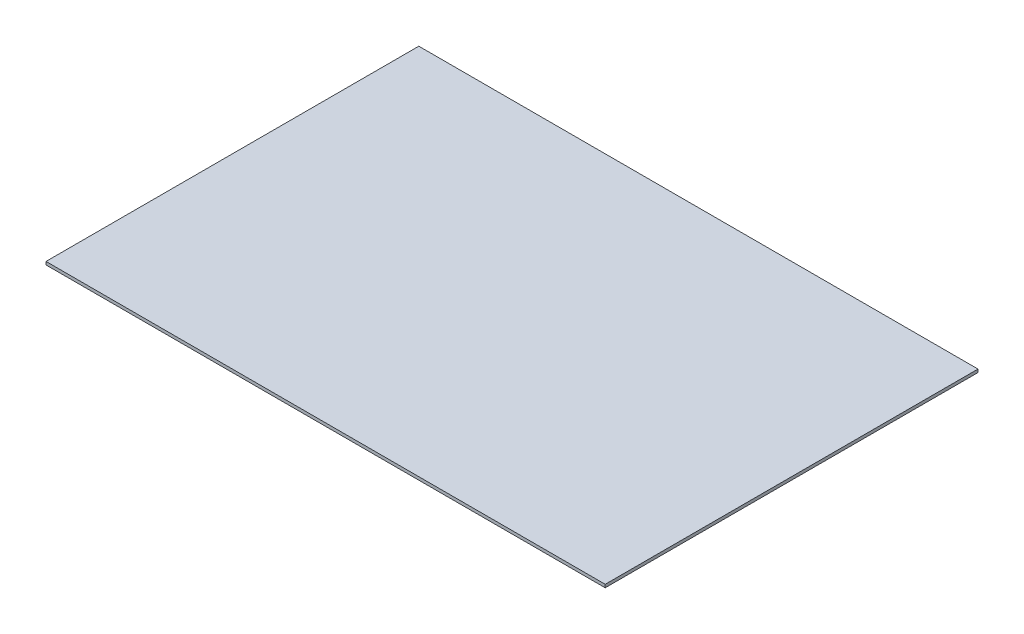
SolidWorks part; units mm, degrees
ref_plane "Спереди" through (0, 0, 0) normal (0, 0, 1) x (1, 0, 0)
ref_plane "Сверху" through (0, 0, 0) normal (0, 1, 0) x (1, 0, 0)
ref_plane "Справа" through (0, 0, 0) normal (1, 0, 0) x (0, 0, -1)
sketch "Эскиз1" plane through (0, 0, 0) normal (0, 1, 0) x (1, 0, 0)
  line L1 (-914.4, -609.6) -> (914.4, -609.6)
  line L2 (-914.4, -609.6) -> (-914.4, 609.6)
  line L3 (-914.4, 609.6) -> (914.4, 609.6)
  line L4 (914.4, -609.6) -> (914.4, 609.6)
  line L5 (-914.4, -609.6) -> (914.4, 609.6) construction
  line L6 (-914.4, 609.6) -> (914.4, -609.6) construction
  point P0 (0, 0)
  dimension "D1" = 1828.8
  dimension "D2" = 1219.2
extrude "Бобышка-Вытянуть1" add sketch "Эскиз1" along normal blind 10
